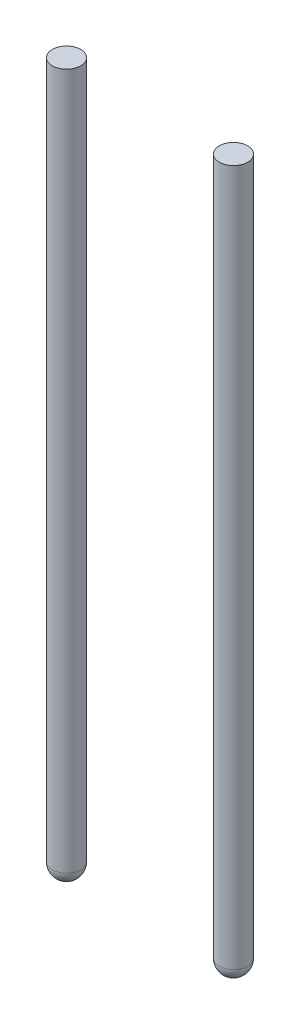
SolidWorks part; units mm, degrees
ref_plane "Front Plane" through (0, 0, 0) normal (0, 0, 1) x (1, 0, 0)
ref_plane "Top Plane" through (0, 0, 0) normal (0, 1, 0) x (1, 0, 0)
ref_plane "Right Plane" through (0, 0, 0) normal (1, 0, 0) x (0, 0, -1)
sketch "Sketch3" plane through (0, 0, 0) normal (0, 1, 0) x (1, 0, 0)
  line L0 (0, 0) -> (1.175, 0) construction
  line L5 (0, 0) -> (-1.175, 0) construction
  circle A0 centre (1.175, 0) radius 0.2
  circle A1 centre (-1.175, 0) radius 0.2
  dimension "D3" = 0.4
  dimension "D4" = 0.4
  dimension "D1" = 1.175
  dimension "D2" = 1.175
extrude "Boss-Extrude1" add sketch "Sketch3" against normal blind 10
fillet "Fillet3" radius 0.2 1 edges at (1.175, -10, 0.2)
fillet "Fillet4" radius 0.2 1 edges at (-1.175, -10, 0.2)
